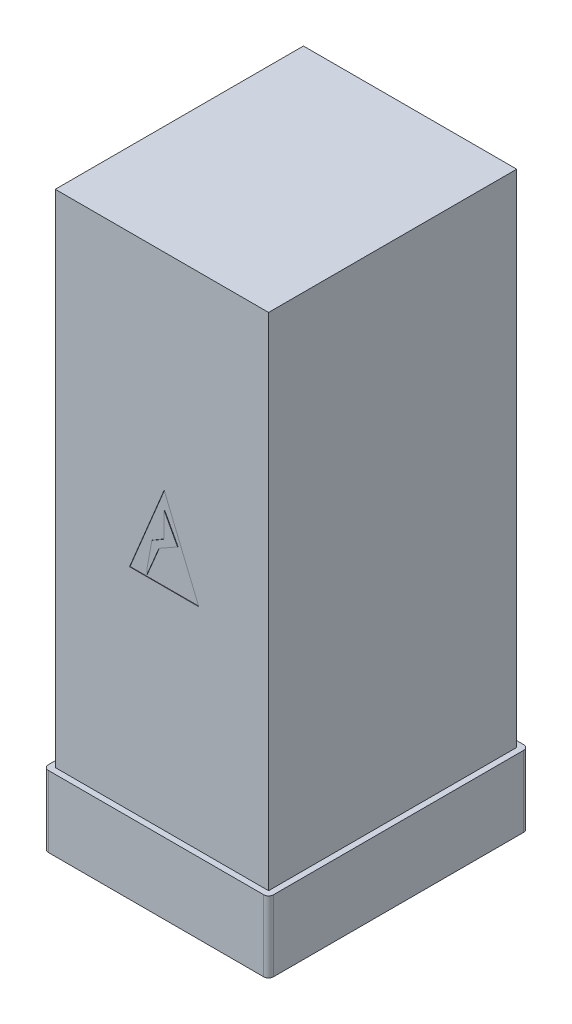
SolidWorks part; units mm, degrees
ref_plane "Alzado" through (0, 0, 0) normal (0, 0, 1) x (1, 0, 0)
ref_plane "Planta" through (0, 0, 0) normal (0, 1, 0) x (1, 0, 0)
ref_plane "Vista lateral" through (0, 0, 0) normal (1, 0, 0) x (0, 0, -1)
sketch "Croquis1" plane through (0, 0, 0) normal (0, 1, 0) x (1, 0, 0)
  line L1 (-450, 523.5) -> (450, 523.5)
  line L2 (-450, 523.5) -> (-450, -523.5)
  line L3 (-450, -523.5) -> (450, -523.5)
  line L4 (450, 523.5) -> (450, -523.5)
  line L5 (-450, 523.5) -> (450, -523.5) construction
  line L6 (-450, -523.5) -> (450, 523.5) construction
  point P0 (0, 0)
  dimension "D1" = 1047
  dimension "D2" = 900
extrude "Saliente-Extruir1" add sketch "Croquis1" along normal blind 2113
shell "Vaciado2" thickness 10
sketch "Croquis2" plane through (0, 0, 523.5) normal (0, 0, 1) x (1, 0, 0)
  line L0 (-440, 2103) -> (440, 2103)
  line L1 (440, 2103) -> (440, 10)
  line L2 (440, 10) -> (-440, 10)
  line L3 (-440, 10) -> (-440, 2103)
extrude "Saliente-Extruir2" add sketch "Croquis2" against normal blind 5
sketch "Croquis3" plane through (0, 0, 523.5) normal (0, 0, 1) x (1, 0, 0)
  line L0 (-136.51, 890.5201) -> (155.4697, 890.5201)
  line L1 (155.4697, 890.5201) -> (9.4799, 1243.171)
  line L2 (9.4799, 1243.171) -> (-136.51, 890.5201)
  line L3 (-63.1768, 920.1946) -> (-42.1695, 1034.0418)
  line L4 (-42.1695, 1034.0418) -> (9.4799, 1064.1699)
  line L5 (9.4799, 1064.1699) -> (9.4799, 1169.412)
  line L6 (9.4799, 1169.412) -> (65.9663, 1064.1699)
  line L7 (65.9663, 1064.1699) -> (-12.5323, 1019.6237)
  line L8 (-12.5323, 1019.6237) -> (-63.1768, 898.9131)
  line L9 (-63.1768, 898.9131) -> (-63.1768, 920.1946)
extrude "Cortar-Extruir1" cut sketch "Croquis3" against normal blind 2
sketch "Croquis4" plane through (0, 0, 0) normal (0, -1, 0) x (1, 0, 0)
  line L0 (-450, -523.5) -> (-450, 523.5) construction
  line L1 (-454.3565, 548.5) -> (454.3565, 548.5)
  line L2 (-475, 527.8565) -> (-475, -527.8565)
  line L3 (-454.3565, -548.5) -> (454.3565, -548.5)
  line L4 (475, 527.8565) -> (475, -527.8565)
  line L5 (-475, 548.5) -> (475, -548.5) construction
  line L6 (-475, -548.5) -> (475, 548.5) construction
  line L7 (-450, 523.5) -> (450, 523.5) construction
  arc A0 (454.3565, 548.5) -> (475, 527.8565) centre (454.3565, 527.8565) cw
  arc A1 (454.3565, -548.5) -> (475, -527.8565) centre (454.3565, -527.8565) ccw
  arc A2 (-475, -527.8565) -> (-454.3565, -548.5) centre (-454.3565, -527.8565) ccw
  arc A3 (-454.3565, 548.5) -> (-475, 527.8565) centre (-454.3565, 527.8565) ccw
  point P0 (0, 0)
  dimension "D3" = 20.6435
  dimension "D1" = 25
  dimension "D2" = 25
extrude "Saliente-Extruir3" add sketch "Croquis4" along normal blind 300
